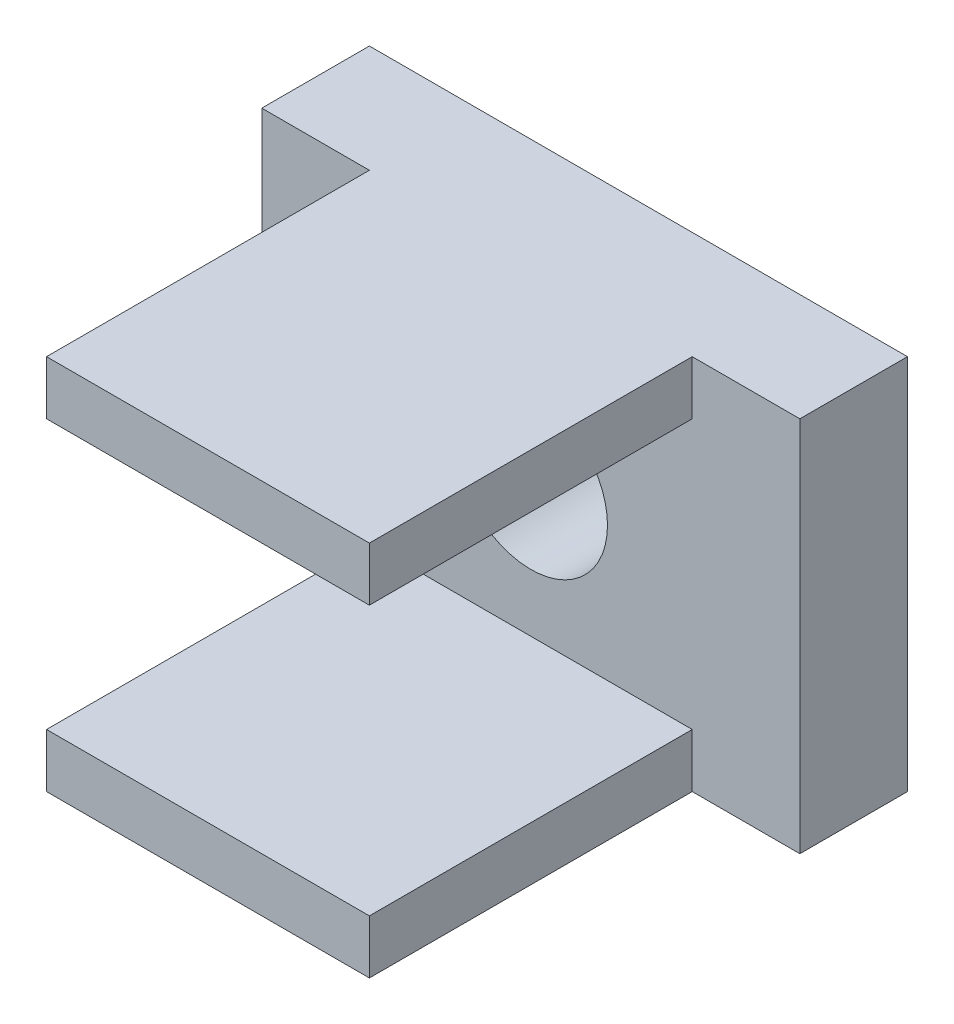
SolidWorks part; units mm, degrees
ref_plane "Front Plane" through (0, 0, 0) normal (0, 0, 1) x (1, 0, 0)
ref_plane "Top Plane" through (0, 0, 0) normal (0, 1, 0) x (1, 0, 0)
ref_plane "Right Plane" through (0, 0, 0) normal (1, 0, 0) x (0, 0, -1)
sketch "Sketch1" plane through (0, 0, 0) normal (0, 0, 1) x (1, 0, 0)
  line L1 (-5, -3.5) -> (5, -3.5)
  line L2 (-5, -3.5) -> (-5, 3.5)
  line L3 (-5, 3.5) -> (5, 3.5)
  line L4 (5, -3.5) -> (5, 3.5)
  line L5 (-5, -3.5) -> (5, 3.5) construction
  line L6 (-5, 3.5) -> (5, -3.5) construction
  point P0 (0, 0)
  dimension "D1" = 10
  dimension "D2" = 7
extrude "Boss-Extrude1" add sketch "Sketch1" along normal blind 2
sketch "Sketch2" plane through (0, 0, 2) normal (0, 0, 1) x (1, 0, 0)
  circle A0 centre (0, 0) radius 1.425
  dimension "D1" = 2.85
extrude "Cut-Extrude1" cut sketch "Sketch2" against normal through all
sketch "Sketch4" plane through (0, 0, 2) normal (0, 0, 1) x (1, 0, 0)
  line L0 (0, -4.5013) -> (0, -5.5013) construction
  line L1 (6.4919, 0) -> (-6.4164, 0) construction
  line L2 (5, 3.5) -> (-5, 3.5) construction
  line L3 (-3, 3.5) -> (3, 3.5)
  line L4 (-3, 3.5) -> (-3, 2.5)
  line L5 (-3, 2.5) -> (3, 2.5)
  line L6 (3, 3.5) -> (3, 2.5)
  line L7 (-3, 3.5) -> (3, 2.5) construction
  line L8 (-3, 2.5) -> (3, 3.5) construction
  line L9 (-3, -2.5) -> (3, -2.5)
  line L10 (3, -3.5) -> (3, -2.5)
  line L11 (-3, -3.5) -> (3, -3.5)
  line L12 (-3, -3.5) -> (-3, -2.5)
  point P5 (0, 3)
  dimension "D1" = 6
  dimension "D2" = 1
extrude "Boss-Extrude3" add sketch "Sketch4" along normal blind 6
